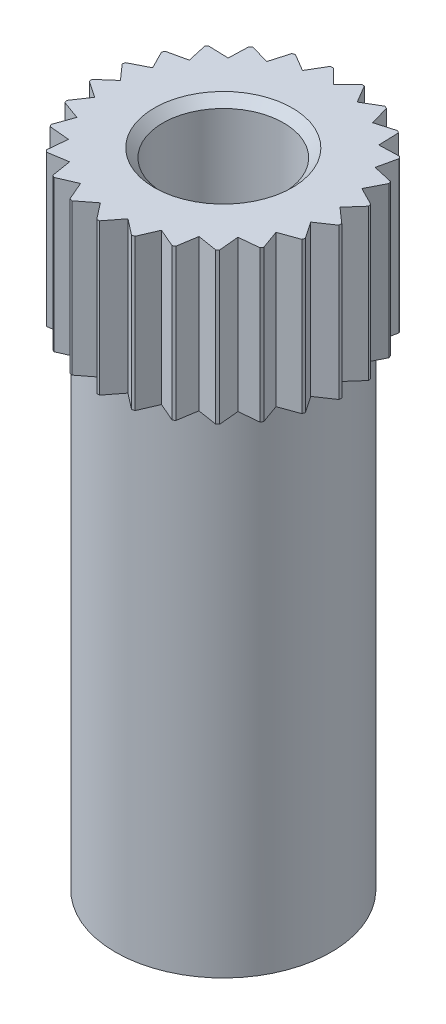
SolidWorks part; units mm, degrees
ref_plane "Front" through (0, 0, 0) normal (0, 0, 1) x (1, 0, 0)
ref_plane "Top" through (0, 0, 0) normal (0, 1, 0) x (1, 0, 0)
ref_plane "Right" through (0, 0, 0) normal (1, 0, 0) x (0, 0, -1)
sketch "Эскиз1" plane through (0, 0, 0) normal (0, 1, 0) x (1, 0, 0)
  circle A0 centre (0, 0) radius 2.9
  dimension "D1" = 5.8
extrude "Бобышка-Вытянуть1" add sketch "Эскиз1" along normal blind 3.5
sketch "Эскиз2" plane through (0, 0, 0) normal (0, -1, 0) x (1, 0, 0)
  circle A0 centre (0, 0) radius 2.5
  dimension "D1" = 5
extrude "Бобышка-Вытянуть2" add sketch "Эскиз2" along normal blind 11.4
sketch "Эскиз3" plane through (0, 3.5, 0) normal (0, 1, 0) x (1, 0, 0)
  line L0 (0, 2.55) -> (-0.3665, 2.9165)
  line L1 (-0.3665, 2.9165) -> (0.3665, 2.9165)
  line L2 (0.3665, 2.9165) -> (0, 2.55)
  line L3 (0.6342, 2.4699) -> (0.3703, 2.916)
  line L4 (0.3703, 2.916) -> (1.0803, 2.7337)
  line L5 (1.0803, 2.7337) -> (0.6342, 2.4699)
  line L6 (1.2285, 2.2346) -> (1.0839, 2.7323)
  line L7 (1.0839, 2.7323) -> (1.7262, 2.3792)
  line L8 (1.7262, 2.3792) -> (1.2285, 2.2346)
  line L9 (1.7456, 1.8589) -> (1.7293, 2.3769)
  line L10 (1.7293, 2.3769) -> (2.2636, 1.8752)
  line L11 (2.2636, 1.8752) -> (1.7456, 1.8589)
  line L12 (2.153, 1.3664) -> (2.2661, 1.8722)
  line L13 (2.2661, 1.8722) -> (2.6589, 1.2533)
  line L14 (2.6589, 1.2533) -> (2.153, 1.3664)
  line L15 (2.4252, 0.788) -> (2.6605, 1.2498)
  line L16 (2.6605, 1.2498) -> (2.887, 0.5527)
  line L17 (2.887, 0.5527) -> (2.4252, 0.788)
  line L18 (2.545, 0.1601) -> (2.8877, 0.5489)
  line L19 (2.8877, 0.5489) -> (2.9338, -0.1826)
  line L20 (2.9338, -0.1826) -> (2.545, 0.1601)
  line L21 (2.5048, -0.4778) -> (2.9335, -0.1865)
  line L22 (2.9335, -0.1865) -> (2.7962, -0.9065)
  line L23 (2.7962, -0.9065) -> (2.5048, -0.4778)
  line L24 (2.3073, -1.0857) -> (2.795, -0.9102)
  line L25 (2.795, -0.9102) -> (2.4829, -1.5734)
  line L26 (2.4829, -1.5734) -> (2.3073, -1.0857)
  line L27 (1.9648, -1.6254) -> (2.4808, -1.5767)
  line L28 (2.4808, -1.5767) -> (2.0136, -2.1414)
  line L29 (2.0136, -2.1414) -> (1.9648, -1.6254)
  line L30 (1.4989, -2.063) -> (2.0108, -2.1441)
  line L31 (2.0108, -2.1441) -> (1.4178, -2.5749)
  line L32 (1.4178, -2.5749) -> (1.4989, -2.063)
  line L33 (0.9387, -2.3709) -> (1.4144, -2.5768)
  line L34 (1.4144, -2.5768) -> (0.7329, -2.8466)
  line L35 (0.7329, -2.8466) -> (0.9387, -2.3709)
  line L36 (0.3196, -2.5299) -> (0.7291, -2.8476)
  line L37 (0.7291, -2.8476) -> (0.0019, -2.9394)
  line L38 (0.0019, -2.9394) -> (0.3196, -2.5299)
  line L39 (-0.3196, -2.5299) -> (-0.0019, -2.9394)
  line L40 (-0.0019, -2.9394) -> (-0.7291, -2.8476)
  line L41 (-0.7291, -2.8476) -> (-0.3196, -2.5299)
  line L42 (-0.9387, -2.3709) -> (-0.7329, -2.8466)
  line L43 (-0.7329, -2.8466) -> (-1.4144, -2.5768)
  line L44 (-1.4144, -2.5768) -> (-0.9387, -2.3709)
  line L45 (-1.4989, -2.063) -> (-1.4178, -2.5749)
  line L46 (-1.4178, -2.5749) -> (-2.0108, -2.1441)
  line L47 (-2.0108, -2.1441) -> (-1.4989, -2.063)
  line L48 (-1.9648, -1.6254) -> (-2.0136, -2.1414)
  line L49 (-2.0136, -2.1414) -> (-2.4808, -1.5767)
  line L50 (-2.4808, -1.5767) -> (-1.9648, -1.6254)
  line L51 (-2.3073, -1.0857) -> (-2.4829, -1.5734)
  line L52 (-2.4829, -1.5734) -> (-2.795, -0.9102)
  line L53 (-2.795, -0.9102) -> (-2.3073, -1.0857)
  line L54 (-2.5048, -0.4778) -> (-2.7962, -0.9065)
  line L55 (-2.7962, -0.9065) -> (-2.9335, -0.1865)
  line L56 (-2.9335, -0.1865) -> (-2.5048, -0.4778)
  line L57 (-2.545, 0.1601) -> (-2.9338, -0.1826)
  line L58 (-2.9338, -0.1826) -> (-2.8877, 0.5489)
  line L59 (-2.8877, 0.5489) -> (-2.545, 0.1601)
  line L60 (-2.4252, 0.788) -> (-2.887, 0.5527)
  line L61 (-2.887, 0.5527) -> (-2.6605, 1.2498)
  line L62 (-2.6605, 1.2498) -> (-2.4252, 0.788)
  line L63 (-2.153, 1.3664) -> (-2.6589, 1.2533)
  line L64 (-2.6589, 1.2533) -> (-2.2661, 1.8722)
  line L65 (-2.2661, 1.8722) -> (-2.153, 1.3664)
  line L66 (-1.7456, 1.8589) -> (-2.2636, 1.8752)
  line L67 (-2.2636, 1.8752) -> (-1.7293, 2.3769)
  line L68 (-1.7293, 2.3769) -> (-1.7456, 1.8589)
  line L69 (-1.2285, 2.2346) -> (-1.7262, 2.3792)
  line L70 (-1.7262, 2.3792) -> (-1.0839, 2.7323)
  line L71 (-1.0839, 2.7323) -> (-1.2285, 2.2346)
  line L72 (-0.6342, 2.4699) -> (-1.0803, 2.7337)
  line L73 (-1.0803, 2.7337) -> (-0.3703, 2.916)
  line L74 (-0.3703, 2.916) -> (-0.6342, 2.4699)
  circle A0 centre (0, 0) radius 2.55 construction
  point P81 (0, 0)
  dimension "D1" = 5.1
  dimension "D2" = 90
  dimension "D3" = 25
extrude "Вырез-Вытянуть1" cut sketch "Эскиз3" against normal blind 4
hole_wizard "Сверло под метчик  спиральное M32" positions "Эскиз8" profile "Эскиз7" hole size "M3x0.5" standard "Din"
sketch "Эскиз8" plane through (0, 3.5, 0) normal (0, 1, 0) x (1, 0, 0)
  point P0 (0, 0)
sketch "Эскиз7" plane through (0, 3.5, 0) normal (1, 0, 0) x (0, 0, 1)
  line L0 (0, 0) -> (0, 8.3)
  line L1 (0, 8.3) -> (1.4, 6.9)
  line L2 (1.4, 6.9) -> (1.4, 0.2)
  line L3 (1.4, 0.2) -> (1.6, 0)
  line L5 (1.6, 0) -> (0, 0)
  line L6 (-1.4, 0.2) -> (-1.6, 0) construction
  line L10 (0, 8.3) -> (-1.4, 6.9) construction
  line L11 (0, -6.35) -> (0, 107.95) construction
  dimension "Диаметр отверстия" = 2.8
  dimension "Глубина отверстия" = 6.9
  dimension "Диаметр передней зенковки" = 3.2
  dimension "Угол передней зенковки" = 90
  dimension "Угол заточки сверла" = 90
